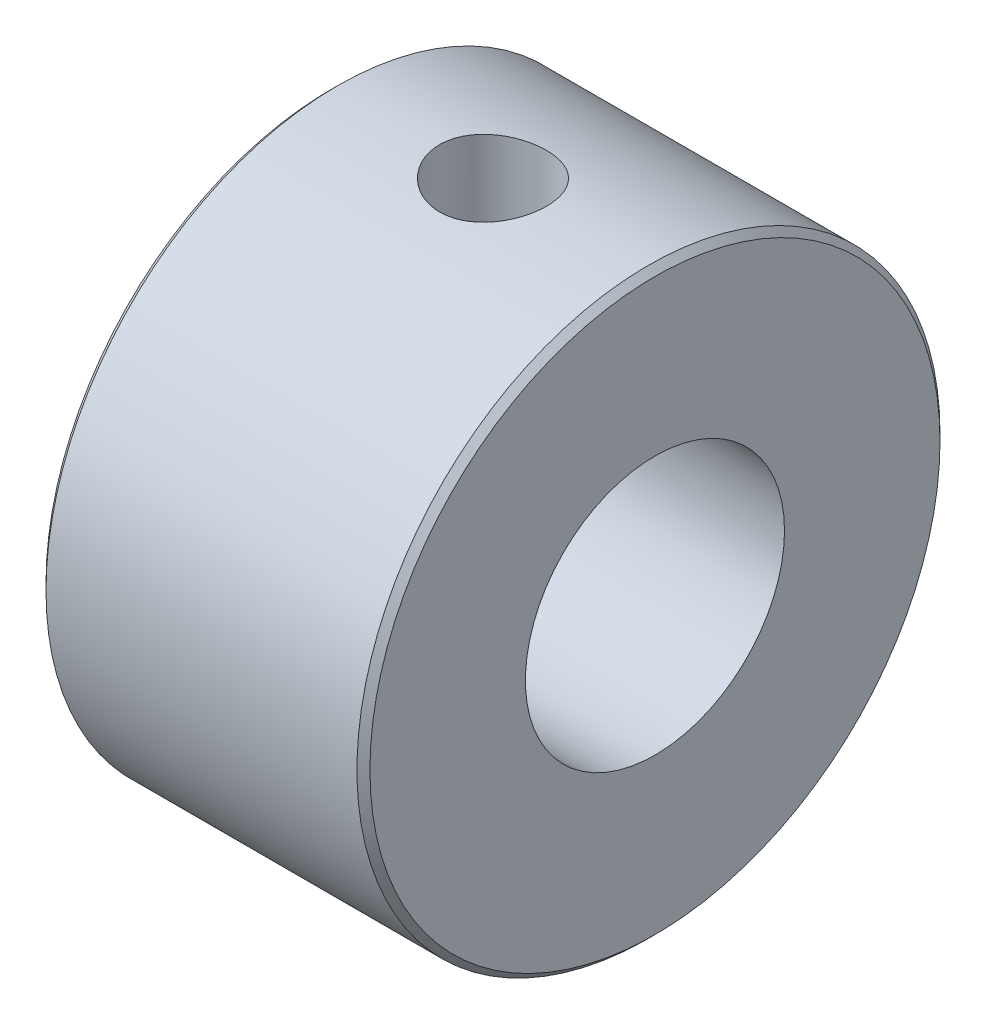
SolidWorks part; units mm, degrees
material "AISI 1020 Steel, Cold Rolled"
ref_plane "Front Plane" through (0, 0, 0) normal (0, 0, 1) x (1, 0, 0)
ref_plane "Top Plane" through (0, 0, 0) normal (0, 1, 0) x (1, 0, 0)
ref_plane "Right Plane" through (0, 0, 0) normal (1, 0, 0) x (0, 0, -1)
sketch "Sketch1" plane through (0, 0, 0) normal (0, 0, 1) x (1, 0, 0)
  line L0 (0, 0) -> (-5, 0) construction
  line L1 (-5, 4) -> (5, 4)
  line L2 (-5, 4) -> (-5, 9)
  line L3 (-5, 9) -> (5, 9)
  line L4 (5, 4) -> (5, 9)
  point P8 (0, 4)
  dimension "D1" = 5
  dimension "D2" = 5
  dimension "D3" = 10
  dimension "D4" = 4
revolve "Revolve1" add sketch "Sketch1" angle 360 about L0
chamfer "Chamfer1" distance 0.2 angle 45 2 edges at (-5, 0, -9) (5, 0, -9)
ref_plane "Plane1" through (0, 9, 0) normal (0, 1, 0) x (1, 0, 0)
hole_wizard "M4 Tapped Hole1" positions "Sketch4" profile "Sketch5" tap size "M4" standard "ISO"
sketch "Sketch4" plane through (0, 9, 0) normal (0, 1, 0) x (1, 0, 0)
  point P0 (0, 0)
sketch "Sketch5" plane through (0, 9, 0) normal (1, 0, 0) x (0, 0, 1)
  line L0 (0, 0) -> (0, 5)
  line L1 (0, 5) -> (1.65, 5)
  line L2 (1.65, 5) -> (1.65, 0)
  line L5 (1.65, 0) -> (0, 0)
  line L11 (0, -6.35) -> (0, 107.95) construction
  dimension "Thru Tap Drill Dia." = 3.3
  dimension "Thru Tap Drill Depth" = 5
cosmetic thread "Hole Thread1"
